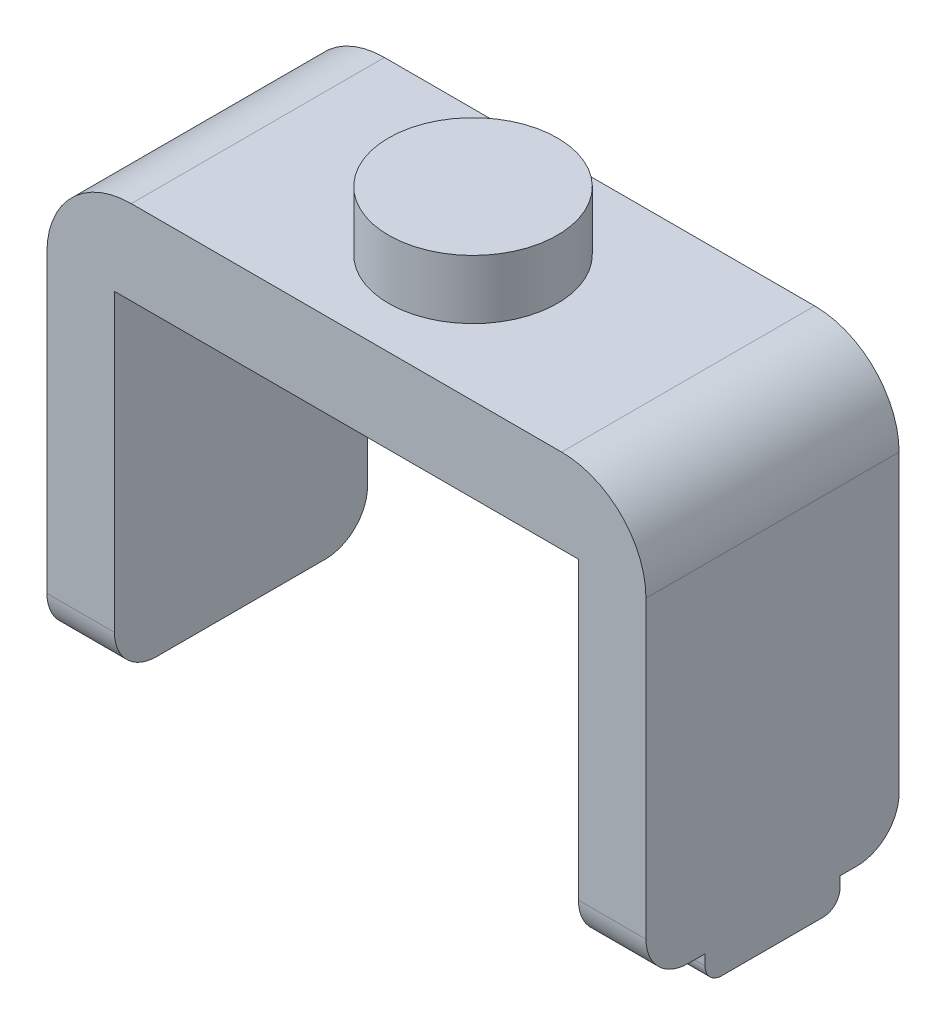
SolidWorks part; units mm, degrees
ref_plane "Front Plane" through (0, 0, 0) normal (0, 0, 1) x (1, 0, 0)
ref_plane "Top Plane" through (0, 0, 0) normal (0, 1, 0) x (1, 0, 0)
ref_plane "Right Plane" through (0, 0, 0) normal (1, 0, 0) x (0, 0, -1)
sketch "Sketch1" plane through (0, 0, 0) normal (0, 0, 1) x (1, 0, 0)
  line L0 (-289.3468, -20.7036) -> (-289.3468, 19.2964)
  line L1 (-289.3468, 19.2964) -> (-234.3468, 19.2964)
  line L2 (-234.3468, 19.2964) -> (-234.3468, -20.7036)
  line L3 (-234.3468, -20.7036) -> (-226.3468, -20.7036)
  line L4 (-226.3468, -20.7036) -> (-226.3468, 29.2964)
  line L5 (-226.3468, 29.2964) -> (-297.3468, 29.2964)
  line L6 (-297.3468, 29.2964) -> (-297.3468, -20.7036)
  line L7 (-297.3468, -20.7036) -> (-289.3468, -20.7036)
  line L9 (-264.3468, 75.6825) -> (-264.3468, -56.7238) construction
  dimension "D1" = 8
  dimension "D2" = 8
  dimension "D3" = 50
  dimension "D5" = 50
  dimension "D6" = 10
  dimension "D7" = 25
  dimension "D8" = 30
extrude "Boss-Extrude1" add sketch "Sketch1" against normal blind 30
sketch "Sketch2" plane through (0, 29.2964, 0) normal (0, 1, 0) x (1, 0, 0)
  line L0 (-226.3468, 15) -> (-261.8468, 15) construction
  line L1 (-226.3468, 30) -> (-226.3468, 0) construction
  line L2 (-261.8468, 15) -> (-261.8468, 0) construction
  line L3 (-226.3468, 0) -> (-297.3468, 0) construction
  circle A1 centre (-261.8468, 15) radius 10
extrude "Boss-Extrude2" add sketch "Sketch2" along normal blind 7
fillet "Fillet1" radius 5
fillet "Fillet2" radius 10
sketch "Sketch3" plane through (0, -20.7036, 0) normal (0, -1, 0) x (1, 0, 0)
  line L0 (-226.3468, -25) -> (-226.3468, -5) construction
  line L1 (-226.3468, -23) -> (-234.3468, -23)
  line L2 (-226.3468, -23) -> (-226.3468, -7)
  line L3 (-226.3468, -7) -> (-234.3468, -7)
  line L4 (-234.3468, -23) -> (-234.3468, -7)
  line L5 (-234.3468, -25) -> (-234.3468, -5) construction
  line L6 (-234.3468, -25) -> (-226.3468, -25) construction
  line L7 (-226.3468, -5) -> (-234.3468, -5) construction
  dimension "D1" = 2
  dimension "D2" = 2
extrude "Boss-Extrude3" add sketch "Sketch3" along normal up to surface (3.25 mm away)
fillet "Fillet3" radius 2
